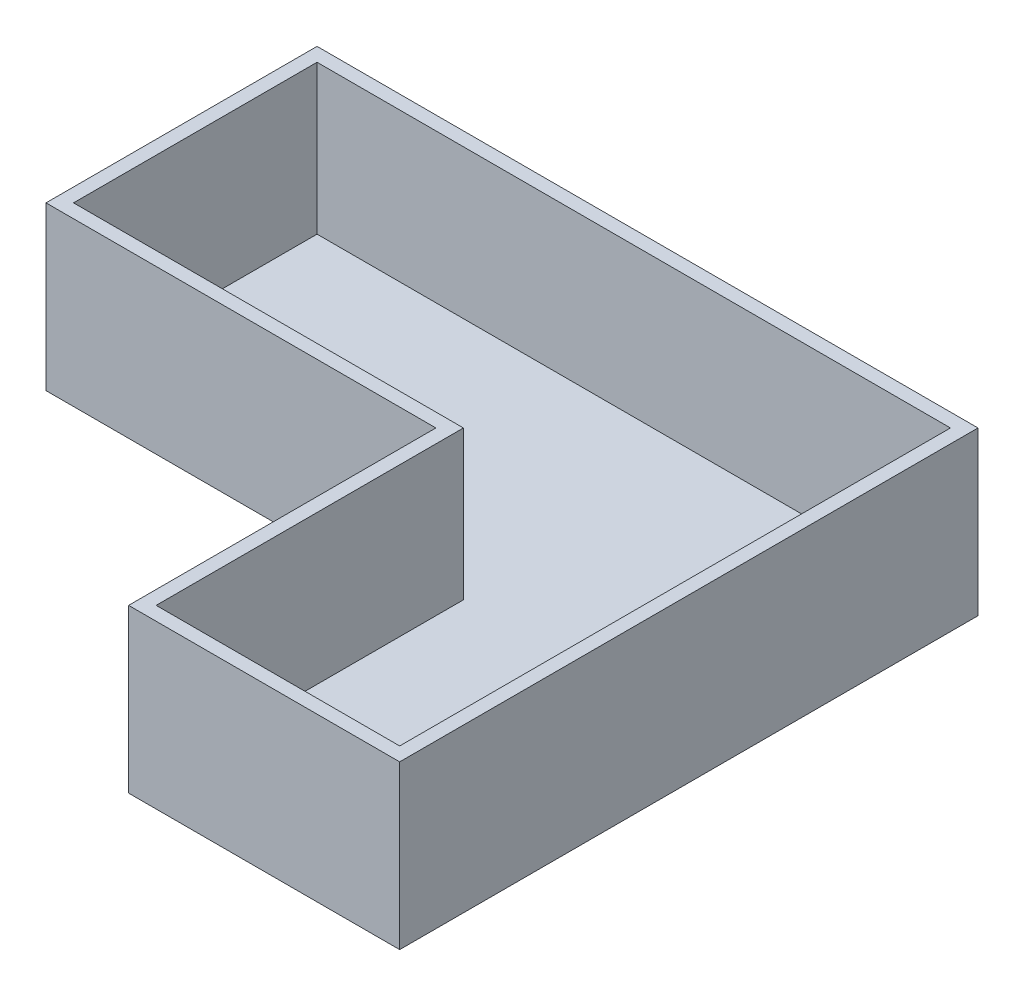
SolidWorks part; units mm, degrees
ref_plane "Front Plane" through (0, 0, 0) normal (0, 0, 1) x (1, 0, 0)
ref_plane "Top Plane" through (0, 0, 0) normal (0, 1, 0) x (1, 0, 0)
ref_plane "Right Plane" through (0, 0, 0) normal (1, 0, 0) x (0, 0, -1)
sketch "Sketch1" plane through (0, 0, 0) normal (0, 1, 0) x (1, 0, 0)
  line L0 (-359.6, 0) -> (359.6, 0) construction
  line L5 (359.6, 1066.8) -> (-359.6, 1066.8)
  line L6 (359.6, 0) -> (859.6, 0)
  line L7 (359.6, 0) -> (359.6, 566.8)
  line L8 (359.6, 1066.8) -> (859.6, 1066.8)
  line L9 (859.6, 0) -> (859.6, 1066.8)
  line L10 (-359.6, 1066.8) -> (-359.6, 566.8)
  line L11 (-359.6, 566.8) -> (359.6, 566.8)
  point P3 (0, 0)
  dimension "D1" = 719.2
  dimension "D2" = 500
  dimension "D3" = 1066.8
  dimension "D4" = 500
extrude "Boss-Extrude1" add sketch "Sketch1" along normal blind 300
sketch "Sketch2" plane through (0, 300, 0) normal (0, 1, 0) x (1, 0, 0)
  line L12 (834.2, 25.4) -> (834.2, 1041.4)
  line L13 (834.2, 1041.4) -> (-334.2, 1041.4)
  line L14 (-334.2, 1041.4) -> (-334.2, 592.2)
  line L15 (-334.2, 592.2) -> (385, 592.2)
  line L16 (385, 592.2) -> (385, 25.4)
  line L17 (385, 25.4) -> (834.2, 25.4)
  line L18 (834.2, 25.4) -> (834.2, 1041.4)
  line L19 (834.2, 1041.4) -> (-334.2, 1041.4)
  line L20 (-334.2, 1041.4) -> (-334.2, 592.2)
  line L21 (-334.2, 592.2) -> (385, 592.2)
  line L22 (385, 592.2) -> (385, 25.4)
  line L23 (385, 25.4) -> (834.2, 25.4)
  dimension "D1" = 25.4
extrude "Cut-Extrude1" cut sketch "Sketch2" against normal blind 274.6
